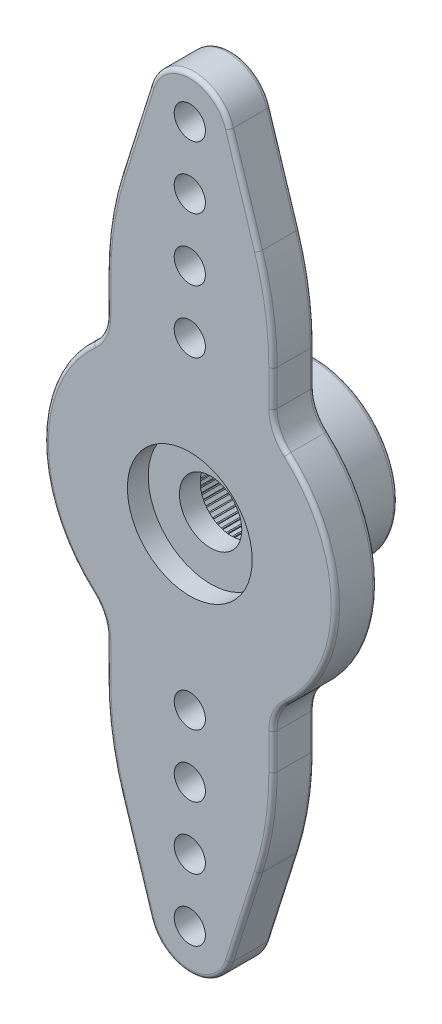
SolidWorks part; units mm, degrees
ref_plane "Ön Düzlem" through (0, 0, 0) normal (0, 0, 1) x (1, 0, 0)
ref_plane "Üst Düzlem" through (0, 0, 0) normal (0, 1, 0) x (1, 0, 0)
ref_plane "Sağ Düzlem" through (0, 0, 0) normal (1, 0, 0) x (0, 0, -1)
sketch "Sketch1" plane through (0, 0, 0) normal (0, 0, 1) x (1, 0, 0)
  line L0 (-4, 10.7446) -> (-4, 5.7446)
  line L1 (4, 10.7446) -> (4, 5.7446)
  line L2 (0, 0) -> (0, 16.75) construction
  line L3 (-4, 5.7446) -> (4, 5.7446) construction
  line L4 (-1.9067, 17.3539) -> (-4, 10.7446)
  line L5 (1.9067, 17.3539) -> (4, 10.7446)
  circle A0 centre (0, 0) radius 7
  circle A1 centre (0, 0) radius 18.75
  circle A2 centre (0, 16.75) radius 2
  circle A3 centre (0, 0) radius 1.5
  dimension "D1" = 37.5
  dimension "D2" = 14
  dimension "D3" = 4
  dimension "D5" = 3
  dimension "D4" = 5
  dimension "D6" = 8
extrude "Boss-Extrude1" add sketch "Sketch1" along normal blind 2 contours A0 A3 | A2 L4 L0 A0 L1 L5 | A2
fillet "Fillet1" radius 15 2 edges at (-4, 10.7446, 1) (4, 10.7446, 1)
sketch "Sketch2" plane through (0, 0, 2) normal (0, 0, 1) x (1, 0, 0)
  line L0 (0, 0) -> (0, 18.75) construction
  arc A0 (1.9067, 17.3539) -> (-1.9067, 17.3539) centre (0, 16.75) ccw construction
  circle A1 centre (0, 16.75) radius 0.75
  circle A2 centre (0, 13.75) radius 0.75
  circle A3 centre (0, 10.75) radius 0.75
  circle A4 centre (0, 7.75) radius 0.75
  dimension "D1" = 1.5
  dimension "D2" = 2
  dimension "D3" = 4
extrude "Cut-Extrude1" cut sketch "Sketch2" against normal through all
pattern_circular "CirPattern2" count 2 over 360 about axis through (0, 0, 0) along (0, 0, 1) of "Boss-Extrude1", "Fillet1", "Cut-Extrude1"
fillet "Fillet2" radius 2 4 edges at (4, 5.7446, 1) (-4, 5.7446, 1) (-4, -5.7446, 1) (4, -5.7446, 1)
sketch "Sketch3" plane through (0, 0, 2) normal (0, 0, 1) x (1, 0, 0)
  circle A0 centre (0, 0) radius 3
  dimension "D1" = 6
extrude "Cut-Extrude2" cut sketch "Sketch3" against normal blind 1
sketch "Sketch4" plane through (0, 0, 0) normal (0, 0, -1) x (-1, 0, 0)
  circle A0 centre (0, 0) radius 4
  circle A1 centre (0, 0) radius 3
  dimension "D1" = 8
  dimension "D2" = 6
extrude "Boss-Extrude2" add sketch "Sketch4" along normal blind 4
sketch "Sketch5" plane through (0, 0, -4) normal (0, 0, -1) x (-1, 0, 0)
  line L0 (0, 0) -> (0, -4) construction
  line L2 (0.025, -2.8941) -> (-0.025, -2.8941)
  line L3 (0.025, -2.8941) -> (0.025, -3.3941)
  line L4 (0.025, -3.3941) -> (-0.025, -3.3941)
  line L5 (-0.025, -2.8941) -> (-0.025, -3.3941)
  line L6 (0.025, -2.8941) -> (-0.025, -3.3941) construction
  line L7 (0.025, -3.3941) -> (-0.025, -2.8941) construction
  circle A1 centre (0, 0) radius 4 construction
  point P0 (0, -3.1441)
  dimension "D1" = 0.05
  dimension "D2" = 0.5
extrude "Boss-Extrude3" add sketch "Sketch5" against normal up to surface (4 mm away) up to face at (-3, 0, 0)
pattern_circular "CirPattern3" count 80 over 360 about axis through (0, 0, 0) along (0, 0, 1) of "Boss-Extrude3"
fillet "Fillet3" radius 0.2 42 edges at (0, 18.75, 0) (-2.6033, 15.1545, 0) (-3.8239, 10.7173, 0) (-4, 7.567, 0) (-4.1743, 5.8917, 0) (-7, 0, 0) (-4.1743, -5.8917, 0) (-4, -7.567, 2) (-4, -7.567, 0) (-3.8239, -10.7173, 2) (-3.8239, -10.7173, 0) (-2.6033, -15.1545, 2) (-2.6033, -15.1545, 0) (0, -18.75, 0) (0, -18.75, 2) (2.6033, -15.1545, 0) (2.6033, -15.1545, 2) (3.8239, -10.7173, 2) (3.8239, -10.7173, 0) (4, -7.567, 0) (4, -7.567, 2) (4.1743, -5.8917, 0) (7, 0, 0) (4.1743, 5.8917, 0) (4, 7.567, 0) (3.8239, 10.7173, 0) (0, 18.75, 2) (-2.6033, 15.1545, 2) (-3.8239, 10.7173, 2) (-4, 7.567, 2) (-4.1743, 5.8917, 2) (-7, 0, 2) (-4.1743, -5.8917, 2) (4.1743, -5.8917, 2) (7, 0, 2) (4.1743, 5.8917, 2) (4, 7.567, 2) (3.8239, 10.7173, 2) (2.6033, 15.1545, 0) (2.6033, 15.1545, 2) (4, 0, 0) (-4, 0, -4)
